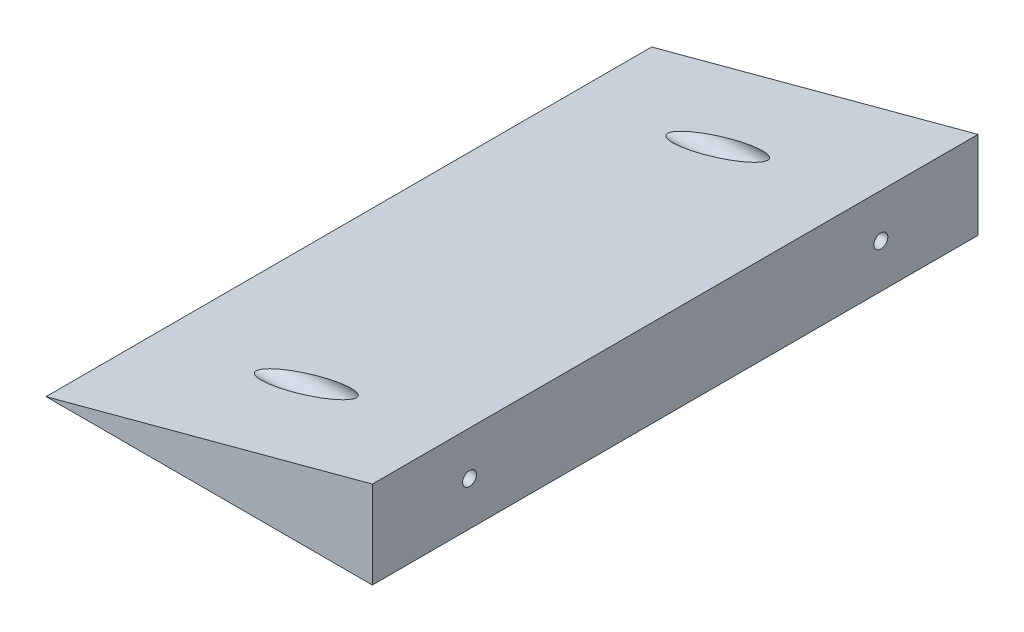
SolidWorks part; units mm, degrees
ref_plane "Front Plane" through (0, 0, 0) normal (0, 0, 1) x (1, 0, 0)
ref_plane "Top Plane" through (0, 0, 0) normal (0, 1, 0) x (1, 0, 0)
ref_plane "Right Plane" through (0, 0, 0) normal (1, 0, 0) x (0, 0, -1)
sketch "Esboço1" plane through (0, 0, 0) normal (0, 0, 1) x (1, 0, 0)
  line L0 (0, 0) -> (0, 27)
  line L1 (0, 27) -> (-100.7654, 0)
  line L2 (0, 0) -> (-100.7654, 0)
  point P3 (-99.6283, 0)
  point P6 (-101.6972, 0)
  dimension "D1" = 27
  dimension "D2" = 75
extrude "Ressalto-extrusão1" add sketch "Esboço1" along normal blind 187
sketch "Esboço2" plane through (-6.75, 25.1913, 0) normal (-0.2588, 0.9659, 0) x (0.9659, 0.2588, 0)
  line L0 (-45.1719, 0) -> (-45.1719, -187) construction
  line L1 (6.9881, 0) -> (-97.3319, 0) construction
  line L2 (6.9881, -187) -> (-97.3319, -187) construction
  line L3 (6.9881, -30) -> (-97.3319, -30) construction
  line L4 (6.9881, -187) -> (6.9881, 0) construction
  line L5 (-97.3319, -187) -> (-97.3319, 0) construction
  line L6 (6.9881, -157) -> (-97.3319, -157) construction
  dimension "D1" = 30
  dimension "D2" = 30
sketch "Esboço6" plane through (0, 0, 0) normal (1, 0, 0) x (0, 0, -1)
  line L0 (-30, 27) -> (-30, 0) construction
  line L1 (-157, 27) -> (-157, 0) construction
  circle A0 centre (-30, 13.5) radius 2.15
  circle A1 centre (-157, 13.5) radius 2.15
  dimension "D1" = 4.3
  dimension "D2" = 4.3
extrude "Corte-extrusão1" cut sketch "Esboço6" against normal through all
ref_plane "Plano1" through (-100, 0, 0) normal (1, 0, 0) x (0, 0, -1)
sketch "Esboço8" plane through (-100, 0, 0) normal (1, 0, 0) x (0, 0, -1)
  circle A2 centre (-30, 13.5) radius 4.15
  circle A3 centre (-30, 13.5) radius 4.15
  circle A5 centre (-157, 13.5) radius 4.15
  circle A6 centre (-157, 13.5) radius 4.15
  dimension "D1" = 2
  dimension "D2" = 2
extrude "Corte-extrusão2" cut sketch "Esboço8" along normal blind 75
